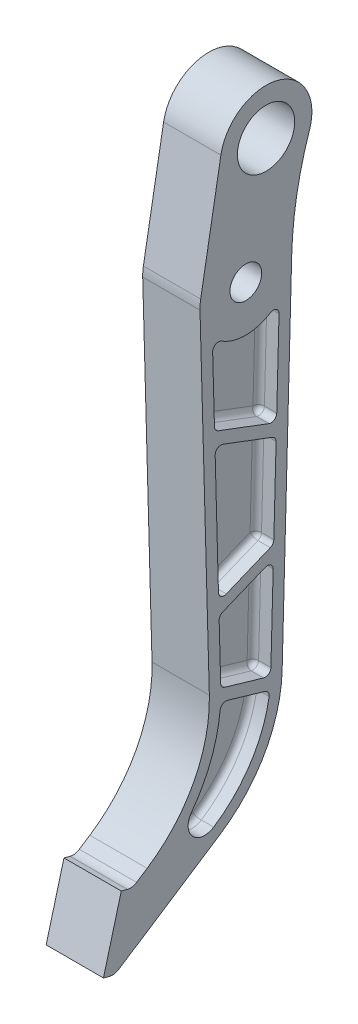
SolidWorks part; units mm, degrees
ref_plane "Front Plane" through (0, 0, 0) normal (0, 0, 1) x (1, 0, 0)
ref_plane "Top Plane" through (0, 0, 0) normal (0, 1, 0) x (1, 0, 0)
ref_plane "Right Plane" through (0, 0, 0) normal (1, 0, 0) x (0, 0, -1)
sketch "Sketch1" plane through (0, 0, 0) normal (1, 0, 0) x (0, 0, -1)
  line L0 (-25.3903, -0.7003) -> (-20.2239, -188.0148)
  line L1 (25.4, 0) -> (20.123, -196.1257)
  line L2 (0, 0) -> (-78.888, -294.4142) construction
  line L3 (0, 0) -> (0, -294.4142) construction
  line L4 (0, -294.4142) -> (-78.888, -294.4142) construction
  line L5 (-60.5169, -257.7014) -> (-54.6821, -253.8847)
  line L6 (-78.888, -294.4142) -> (-75.4975, -295.3227)
  line L7 (-78.888, -294.4142) -> (-69.027, -257.6124)
  line L8 (-69.027, -257.6124) -> (-65.6365, -258.5209)
  line L9 (-72.7544, -296.0577) -> (-62.8934, -259.2559) construction
  line L10 (-70.3779, -294.5031) -> (-14.3366, -257.8451)
  line L11 (0, 0) -> (11.1968, 63.5) construction
  line L12 (0, 0) -> (25.4, 0) construction
  line L13 (11.1968, 63.5) -> (11.1968, 0) construction
  line L14 (-13.8174, 67.9107) -> (-25.0141, 4.4107)
  circle A0 centre (0, 0) radius 8.8004
  arc A2 (-54.6821, -253.8847) -> (-20.2239, -188.0148) centre (-96.395, -190.1158) ccw
  arc A3 (-14.3366, -257.8451) -> (20.123, -196.1257) centre (-56.0494, -194.0762) ccw
  arc A4 (-70.3779, -294.5031) -> (-75.4975, -295.3227) centre (-73.854, -289.1891) cw
  arc A5 (-60.5169, -257.7014) -> (-65.6365, -258.5209) centre (-63.993, -252.3873) cw
  arc A8 (35.2622, 55.3751) -> (25.4, 0) centre (214.3367, -5.0835) ccw
  arc A9 (35.2622, 55.3751) -> (-13.8174, 67.9107) centre (11.1968, 63.5) ccw
  circle A10 centre (11.1968, 63.5) radius 15.875
  arc A11 (-25.0141, 4.4107) -> (-25.3903, -0.7003) centre (0, 0) ccw
  point P17 (-19.05, -230.5769)
  point P20 (19.05, -236.0062)
  dimension "D1" = 17.6007
  dimension "D2" = 25.4
  dimension "D7" = 76.2
  dimension "D8" = 76.2
  dimension "D12" = 6.35
  dimension "D13" = 6.35
  dimension "D14" = 25.4
  dimension "D17" = 31.75
  dimension "D3" = 304.8
  dimension "D4" = 15
  dimension "D5" = 38.1
  dimension "D6" = 6.35
  dimension "D9" = 19.05
  dimension "D10" = 19.05
  dimension "D11" = 25.4
  dimension "D15" = 10
  dimension "D16" = 63.5
  dimension "D18" = 25.4
extrude "Boss-Extrude1" add sketch "Sketch1" along normal mid plane 31.75
sketch "Sketch2" plane through (15.875, 0, 0) normal (1, 0, 0) x (0, 0, -1)
  line L0 (-11.6603, -188.4901) -> (9.8183, -194.7936)
  line L1 (-18.3877, -24.2757) -> (18.3947, -24.2692) construction
  line L2 (0.0035, -24.2725) -> (-0.921, -191.6419) construction
  line L3 (-16.082, -107.8709) -> (16.1405, -108.0489) construction
  line L4 (15.5153, -131.2875) -> (16.7658, -84.8102)
  line L5 (-15.1742, -141.2921) -> (-16.9898, -74.4496)
  line L6 (-10.7935, -144.1426) -> (13.5483, -134.1388)
  line L7 (-12.6932, -71.3935) -> (14.7147, -81.7549)
  line L8 (-15.3313, -63.6076) -> (12.8308, -74.2541)
  line L9 (-14.77, -63.8198) -> (19.139, -76.6389) construction
  line L10 (-18.3877, -24.2757) -> (-17.3823, -60.7253)
  line L11 (17.1274, -71.3697) -> (18.3947, -24.2692)
  line L12 (-12.8189, -151.8403) -> (10.761, -142.1497)
  line L13 (-12.9293, -151.8857) -> (17.6096, -139.3351) construction
  line L14 (-14.7858, -154.8646) -> (-13.94, -185.5312)
  line L15 (13.8862, -191.8325) -> (15.1417, -145.1717)
  line L16 (-19.0428, -0.5252) -> (-13.8763, -187.8398)
  line L17 (-51.206, -259.1988) -> (-57.0408, -263.0155)
  line L18 (-64.4537, -265.0789) -> (-70.2892, -286.8572)
  line L19 (-70.2892, -286.8572) -> (-17.8126, -252.5311)
  line L20 (13.7753, -195.9549) -> (19.0523, 0.1708)
  line L21 (-7.5638, 66.808) -> (-18.7606, 3.308)
  line L22 (-18.3877, -24.2757) -> (-13.8763, -187.8398) construction
  line L26 (13.7753, -195.9549) -> (18.3947, -24.2692) construction
  line L28 (-15.3431, -146.0124) -> (15.1958, -133.4617) construction
  line L29 (-17.0155, -69.7595) -> (16.8936, -82.5786) construction
  line L30 (-10.1952, -195.5379) -> (10.6667, -201.6604)
  line L31 (-13.4485, -194.5832) -> (8.0301, -200.8866) construction
  arc A0 (-30.1717, -239.4004) -> (-17.8126, -252.5311) centre (-22.8255, -244.8676) ccw
  arc A1 (9.8183, -194.7936) -> (13.8862, -191.8325) centre (10.7124, -191.7471) ccw
  arc A2 (-11.6603, -188.4901) -> (-13.94, -185.5312) centre (-10.7662, -185.4436) cw
  arc A3 (-12.8189, -151.8403) -> (-14.7858, -154.8646) centre (-11.6121, -154.777) ccw
  arc A4 (10.761, -142.1497) -> (15.1417, -145.1717) centre (11.9678, -145.0863) cw
  arc A5 (15.5153, -131.2875) -> (13.5483, -134.1388) centre (12.3414, -131.2021) cw
  arc A6 (-15.1742, -141.2921) -> (-10.7935, -144.1426) centre (-12.0004, -141.2059) ccw
  arc A8 (-13.5235, -21.5006) -> (13.5297, -21.4967) centre (0, 0) ccw
  arc A9 (-25.0141, 4.4107) -> (-25.3903, -0.7003) centre (0, 0) ccw construction
  arc A10 (18.3947, -24.2692) -> (13.5297, -21.4967) centre (15.2209, -24.1838) ccw
  arc A11 (-18.3877, -24.2757) -> (-13.5235, -21.5006) centre (-15.2139, -24.1882) cw
  arc A14 (-18.7606, 3.308) -> (-19.0428, -0.5252) centre (0, 0) ccw
  arc A15 (-51.206, -259.1988) -> (-13.8763, -187.8398) centre (-96.395, -190.1158) ccw
  arc A16 (-64.4537, -265.0789) -> (-57.0408, -263.0155) centre (-63.993, -252.3873) ccw
  arc A17 (-17.8126, -252.5311) -> (13.7753, -195.9549) centre (-56.0494, -194.0762) ccw
  arc A18 (29.2458, 57.4063) -> (19.0523, 0.1708) centre (214.3367, -5.0835) ccw
  arc A19 (29.2458, 57.4063) -> (-7.5638, 66.808) centre (11.1968, 63.5) ccw
  arc A21 (-30.1717, -239.4004) -> (-13.8763, -187.8398) centre (-96.395, -190.1158) ccw construction
  arc A23 (-17.8126, -252.5311) -> (13.7753, -195.9549) centre (-56.0494, -194.0762) ccw construction
  arc A24 (16.7658, -84.8102) -> (14.7147, -81.7549) centre (13.5919, -84.7248) ccw
  arc A25 (-12.6932, -71.3935) -> (-16.9898, -74.4496) centre (-13.8159, -74.3634) ccw
  arc A26 (12.8308, -74.2541) -> (17.1274, -71.3697) centre (13.9536, -71.2843) ccw
  arc A27 (-15.3313, -63.6076) -> (-17.3823, -60.7253) centre (-14.2086, -60.6377) cw
  arc A28 (-14.2488, -198.2708) -> (-30.1717, -239.4004) centre (-96.395, -190.1158) cw
  arc A29 (12.907, -205.2132) -> (-17.8126, -252.5311) centre (-56.0494, -194.0762) cw
  arc A30 (10.6667, -201.6604) -> (12.907, -205.2132) centre (9.7727, -204.7069) cw
  arc A31 (-10.1952, -195.5379) -> (-14.2488, -198.2708) centre (-11.0893, -198.5844) ccw
  point P14 (-0.4587, -107.9572)
  point P21 (16.1405, -108.0489)
  point P25 (-16.082, -107.8709)
  point P48 (-14.8463, -152.6735)
  point P52 (15.2729, -140.2954)
  point P63 (15.4597, -133.3533)
  point P70 (16.8265, -82.5533)
  point P76 (17.0073, -75.833)
  point P79 (-17.3236, -62.8544)
  point P86 (13.2989, -202.4329)
  point P89 (-13.958, -194.4336)
  dimension "D2" = 3.175
  dimension "D3" = 9.1573
  dimension "D8" = 3.175
  dimension "D11" = 3.175
  dimension "D4" = 13.5766
  dimension "D5" = 66.8426
  dimension "D6" = 6.35
  dimension "D7" = 6.35
  dimension "D9" = 46.4774
  dimension "D10" = 6.35
  dimension "D1" = 6.35
extrude "Cut-Extrude1" cut sketch "Sketch2" against normal blind 10
fillet "Fillet1" radius 3.175 30 edges at (5.875, -195.9518, 12.8641) (5.875, -198.5992, -0.2358) (5.875, -203.0134, -12.4583) (5.875, -232.1114, -2.5368) (5.875, -251.144, 29.4936) (5.875, -219.9187, 19.4126) (5.875, -191.6419, 0.921) (5.875, -187.3814, 13.2813) (5.875, -170.1979, 14.3629) (5.875, -153.046, 14.2736) (5.875, -146.995, 1.029) (5.875, -142.4729, -13.7708) (5.875, -168.5021, -14.514) (5.875, -194.314, -12.5809) (5.875, -139.1407, -1.3774) (5.875, -143.8672, 13.732) (5.875, -107.8709, 16.082) (5.875, -71.7761, 15.6562) (5.875, -76.5742, -1.0107) (5.875, -82.9551, -16.228) (5.875, -108.0489, -16.1405) (5.875, -133.005, -14.9549) (5.875, -47.8194, -17.7611) (5.875, -73.9203, -15.7233) (5.875, -68.9309, 1.2502) (5.875, -62.4785, 16.7954) (5.875, -42.5005, 17.885) (5.875, -21.4304, 16.7872) (5.875, -25.4, -0.0037) (5.875, -21.4253, -16.7929)
mirror "Mirror2" about plane through (0, 0, 0) normal (1, 0, 0) of "Fillet1", "Cut-Extrude1"
